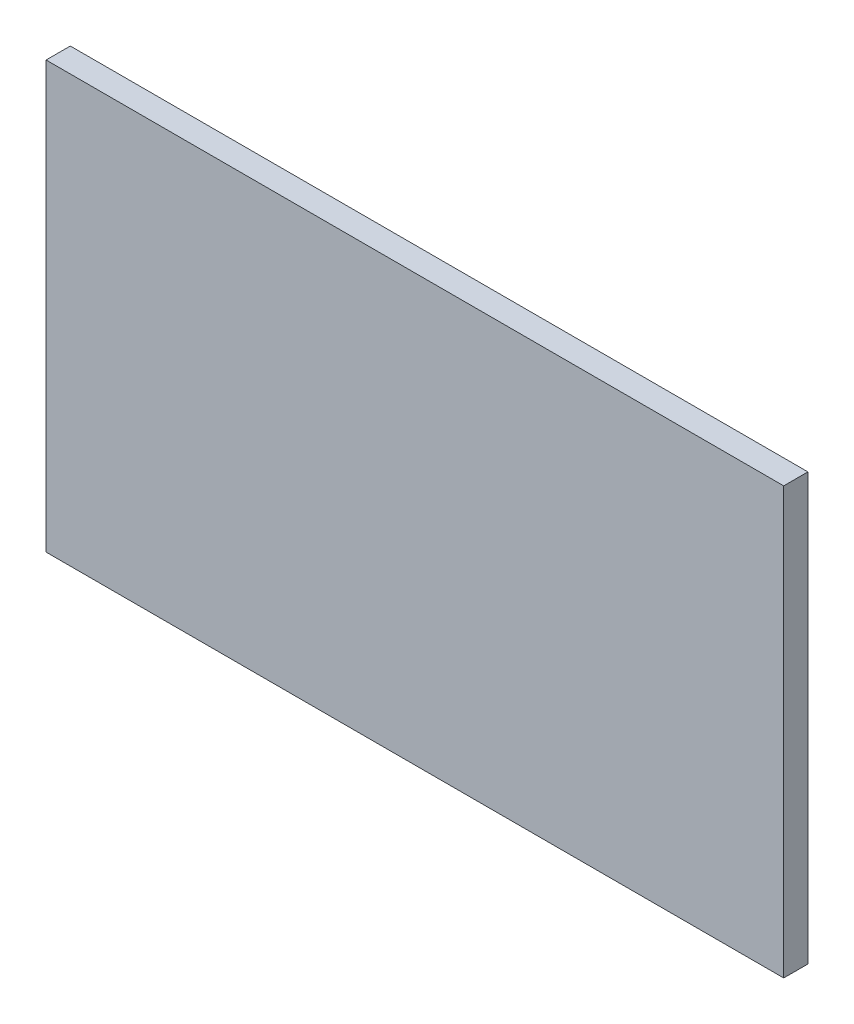
SolidWorks part; units mm, degrees
material "AISI 316 Annealed Stainless Steel Bar (SS)"
ref_plane "Front Plane" through (0, 0, 0) normal (0, 0, 1) x (1, 0, 0)
ref_plane "Top Plane" through (0, 0, 0) normal (0, 1, 0) x (1, 0, 0)
ref_plane "Right Plane" through (0, 0, 0) normal (1, 0, 0) x (0, 0, -1)
sketch "Sketch1" plane through (0, 0, 0) normal (0, 0, 1) x (1, 0, 0)
  line L1 (0, 0) -> (193.49, 0)
  line L2 (0, 0) -> (0, 111.8)
  line L3 (0, 111.8) -> (193.49, 111.8)
  line L4 (193.49, 0) -> (193.49, 111.8)
  dimension "D1" = 193.49
  dimension "D2" = 111.8
extrude "Boss-Extrude1" add sketch "Sketch1" along normal blind 6.35
